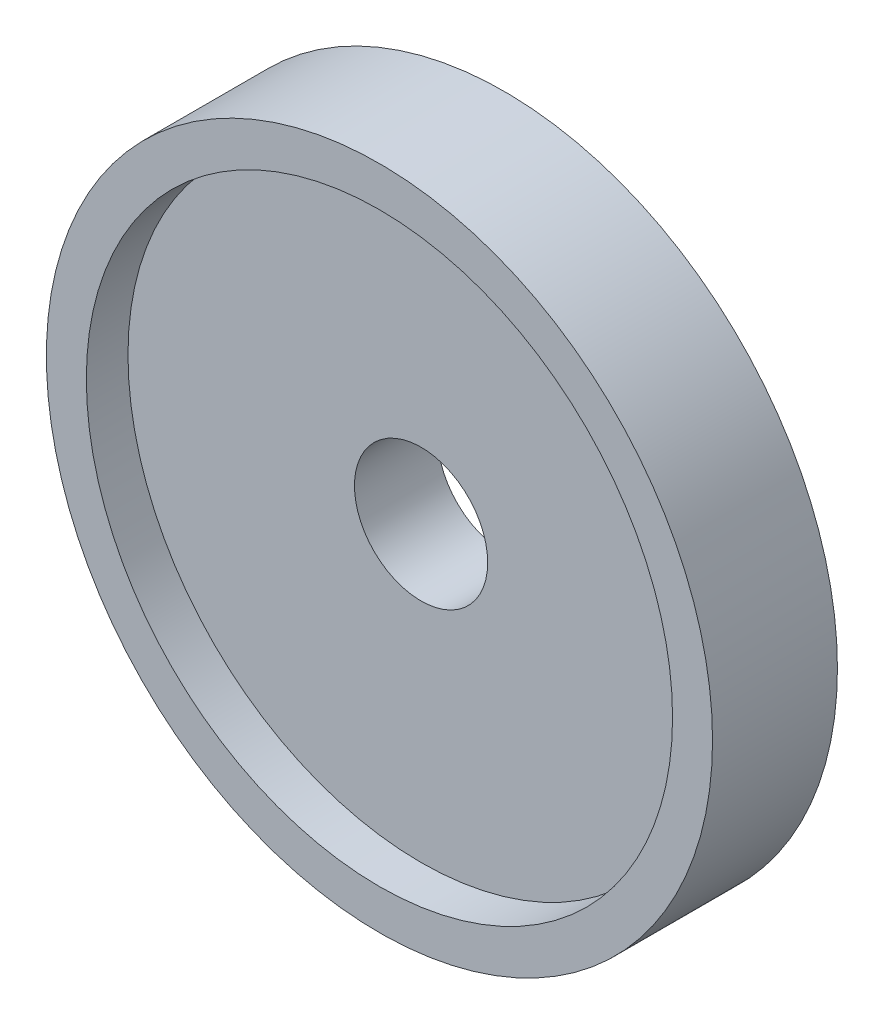
SolidWorks part; units mm, degrees
ref_plane "Front Plane" through (0, 0, 0) normal (0, 0, 1) x (1, 0, 0)
ref_plane "Top Plane" through (0, 0, 0) normal (0, 1, 0) x (1, 0, 0)
ref_plane "Right Plane" through (0, 0, 0) normal (1, 0, 0) x (0, 0, -1)
sketch "Sketch1" plane through (0, 0, 0) normal (0, 1, 0) x (1, 0, 0)
  line L0 (2, -0.75) -> (2, 0)
  line L1 (2, 0) -> (0.4, 0)
  line L2 (0.4, 0) -> (0.4, -0.5)
  line L3 (0.4, -0.5) -> (1.76, -0.5)
  line L4 (1.76, -0.5) -> (1.76, -0.75)
  line L5 (1.76, -0.75) -> (2, -0.75)
  line L6 (0, 0) -> (0, -0.75) construction
revolve "Revolve1" add sketch "Sketch1" angle 360 about L6
